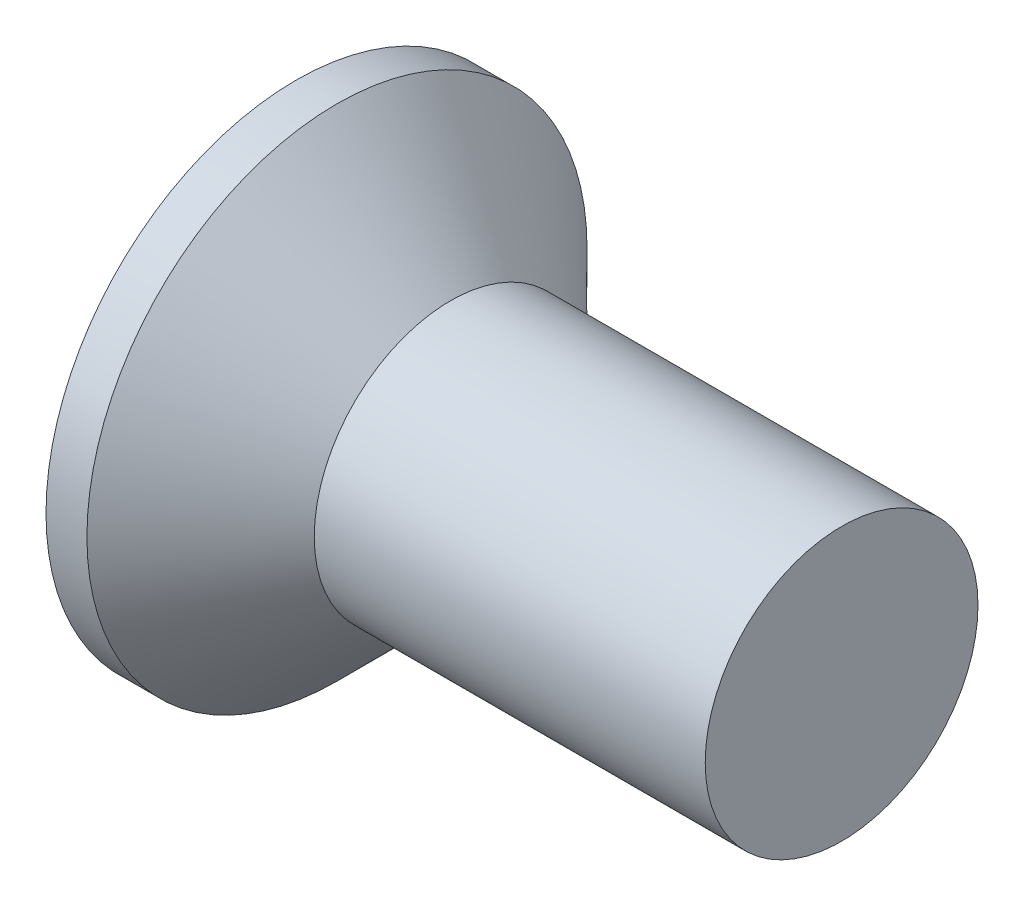
SolidWorks part; units mm, degrees
ref_plane "Plane1" through (0, 0, 0) normal (0, 0, 1) x (1, 0, 0)
ref_plane "Plane2" through (0, 0, 0) normal (0, 1, 0) x (1, 0, 0)
ref_plane "Plane3" through (0, 0, 0) normal (1, 0, 0) x (0, 0, -1)
sketch "BodySke" plane through (0, 0, 0) normal (0, 0, 1) x (1, 0, 0)
  line L0 (0, 0) -> (0, 2.75)
  line L1 (0, 2.75) -> (0.45, 2.75)
  line L2 (1.7, 1.5) -> (6, 1.5)
  line L3 (6, 1.5) -> (6, 0)
  line L4 (6, 0) -> (0, 0)
  line L5 (-6.35, 0) -> (82.55, 0) construction
  line L6 (1.7, -1.5) -> (6, -1.5) construction
  line L7 (0.45, -2.75) -> (1.7, -1.5) construction
  line L8 (0.45, 2.75) -> (1.7, 1.5)
  line L9 (0, -2.75) -> (0.45, -2.75) construction
  line L10 (2.2, 3.0875) -> (2.2, -6.4375) construction
  line L11 (0, 6.35) -> (0, -3.175) construction
  dimension "Diameter" = 3
  dimension "Length" = 6
  dimension "Head_ht" = 1.7
  dimension "Head_dia" = 5.5
  dimension "Head_ang" = 90
  dimension "D6" = 0.45
  dimension "Advance" = 0.5
  dimension "Thread_nom" = 6
revolve "Base-Revolve" add sketch "BodySke" angle 360 about L5
cosmetic thread "ThreadCosmetic" [suppressed] parameters "Thread_length"=3.8, "Thread_minor"=2.439
sketch "Sketch2" [suppressed] plane through (0, 0, 0) normal (-1, 0, 0) x (0, 0, 1)
  line L0 (-1.9, -0.35) -> (1.9, -0.35)
  line L1 (-1.9, -0.35) -> (-1.9, 0.35)
  line L2 (1.9, 0.35) -> (-1.9, 0.35)
  line L3 (1.9, 0.35) -> (1.9, -0.35)
  dimension "D1" = 0.5
  dimension "Slot_width" = 1
  dimension "D2" = 5.5
  dimension "D3" = 2.75
extrude "Slot" [suppressed] cut sketch "Sketch2" against normal blind 0.9
sketch "Sketch3" plane through (0, 0, 0) normal (-1, 0, 0) x (0, 0, 1)
  line L0 (-0.395, 1.55) -> (0.395, 1.55)
  line L1 (0.395, 1.55) -> (0.395, -1.55)
  line L2 (0.395, -1.55) -> (-0.395, -1.55)
  line L3 (-0.395, -1.55) -> (-0.395, 1.55)
  dimension "D1" = 1.55
  dimension "Cross_dia" = 3.1
  dimension "D2" = 0.395
  dimension "Cross_width" = 0.79
ref_plane "Plane4" through (2.08, 0, 0) normal (-1, 0, 0) x (0, 0, 1)
sketch "Sketch4" plane through (2.08, 0, 0) normal (-1, 0, 0) x (0, 0, 1)
  line L0 (-0.1975, 0.1975) -> (0.1975, 0.1975)
  line L3 (0.1975, 0.1975) -> (0.1975, -0.1975)
  line L4 (0.1975, -0.1975) -> (-0.1975, -0.1975)
  line L5 (-0.1975, -0.1975) -> (-0.1975, 0.1975)
  dimension "D1" = 0.395
  dimension "D2" = 0.395
  dimension "D3" = 0.1975
  dimension "D4" = 0.1975
loft "Cross" cut profiles "Sketch3", "Sketch4"
pattern_circular "CirPattern1" count 2 every 90 about axis through (0, 0, 0) along (1, 0, 0) of "Cross"
sketch "ThdSchSke" [suppressed] plane through (0, 0, 0) normal (0, 0, 1) x (1, 0, 0)
  line L0 (5.85, -3.3095) -> (5.3665, -4)
  line L1 (5.85, -3.3095) -> (6.3335, -4)
  line L2 (6.3335, -4) -> (6.3335, -5)
  line L3 (-3.175, 0) -> (5.1513, 0) construction
  line L5 (6.3335, -5) -> (5.3665, -5)
  line L6 (5.3665, -5) -> (5.3665, -4)
  line L7 (0, 7.9) -> (0, -7.9) construction
  dimension "Thread_minor" = 2.439
  dimension "Diameter" = 3
  dimension "Start" = 2.2
  dimension "SideAngle" = 55
  dimension "VeeAngle" = 70
  dimension "Overcut" = 3.75
revolve "ThreadSchematic" [suppressed] cut sketch "ThdSchSke" angle 360 about L3
pattern_linear "ThdSchPat" [suppressed]
equation "\"D1@Sketch3\" = \"Cross_dia@Sketch3\" / 2"
equation "\"D2@Sketch3\" = \"Cross_width@Sketch3\" / 2"
equation "\"D1@Sketch4\" = \"Cross_width@Sketch3\" *.5"
equation "\"D2@Sketch4\" = \"D1@Sketch4\""
equation "\"D4@Sketch4\" = \"D2@Sketch4\" / 2"
equation "\"D3@Sketch4\" = \"D1@Sketch4\" / 2"
equation "\"D1@Sketch2\" = \"Slot_width@Sketch2\" / 2"
equation "\"D2@Sketch2\" = \"Head_dia@BodySke\""
equation "\"D3@Sketch2\" = \"D2@Sketch2\" / 2"
equation "\"Thread_length@ThreadCosmetic\" = ((sgn( (\"Length@BodySke\" - \"Advance@BodySke\" - \"Head_ht@BodySke\" ) - \"Thread_nom@BodySke\" )-1)*( (\"Length@BodySke\" - \"Advance@BodySke\" - \"Head_ht@BodySke\" ) - \"Thread_nom@BodySke\" ))/-2+ \"Thread_nom@BodySke\""
equation "\"Thread_minor@ThdSchSke\" = \"Thread_minor@ThreadCosmetic\""
equation "\"Diameter@ThdSchSke\" = \"Diameter@BodySke\""
equation "\"Overcut@ThdSchSke\" = \"Diameter@BodySke\" * 1.25"
equation "\"Start@ThdSchSke\" = 0.000001 + \"Length@BodySke\" - \"Thread_length@ThreadCosmetic\"  '---Countersunk---"
equation "\"Num_threads@ThdSchPat\" = int( \"Thread_length@ThreadCosmetic\" / \"Advance@BodySke\" + 0.999 )  + 1"
equation "\"Advance@ThdSchPat\" = \"Thread_length@ThreadCosmetic\" /  (\"Num_threads@ThdSchPat\" - 1) 'relax it"
